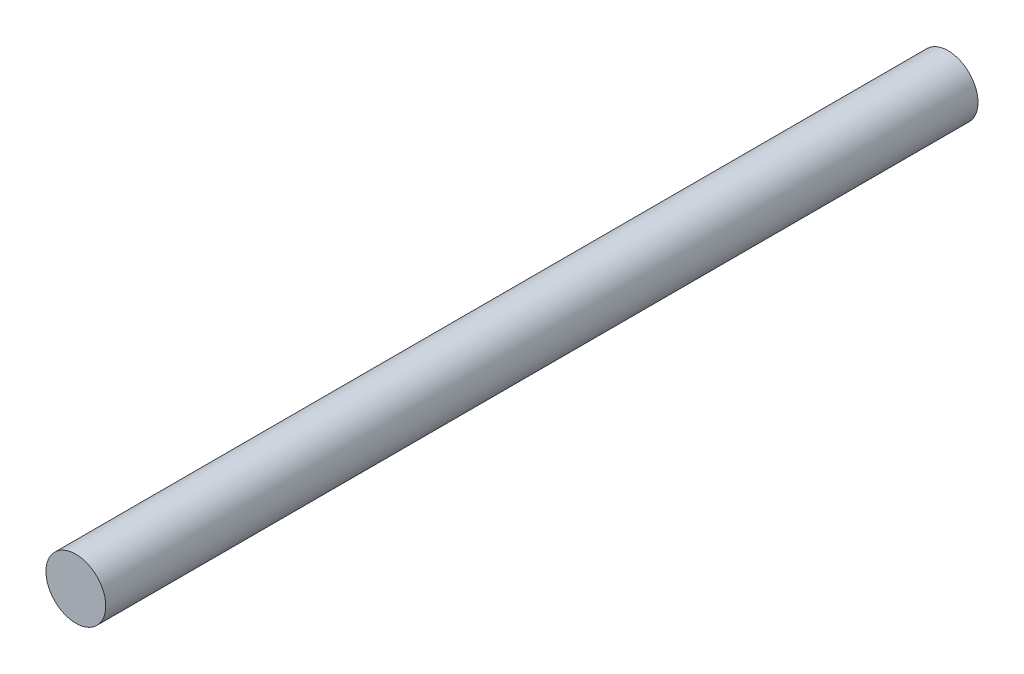
SolidWorks part; units mm, degrees
material "ABS"
ref_plane "Front Plane" through (0, 0, 0) normal (0, 0, 1) x (1, 0, 0)
ref_plane "Top Plane" through (0, 0, 0) normal (0, 1, 0) x (1, 0, 0)
ref_plane "Right Plane" through (0, 0, 0) normal (1, 0, 0) x (0, 0, -1)
sketch "Sketch1" plane through (0, 0, 0) normal (0, 0, 1) x (1, 0, 0)
  circle A0 centre (0, 0) radius 2.4
  dimension "D1" = 4.8
extrude "Boss-Extrude1" add sketch "Sketch1" along normal mid plane 70
